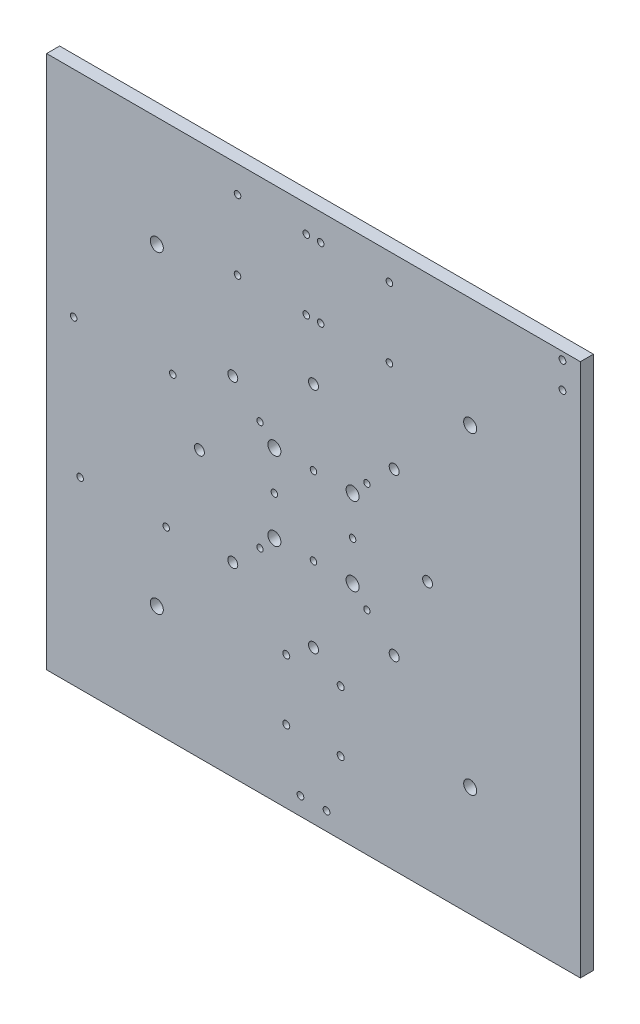
SolidWorks part; units mm, degrees
ref_plane "Front Plane" through (0, 0, 0) normal (0, 0, 1) x (1, 0, 0)
ref_plane "Top Plane" through (0, 0, 0) normal (0, 1, 0) x (1, 0, 0)
ref_plane "Right Plane" through (0, 0, 0) normal (1, 0, 0) x (0, 0, -1)
sketch "Sketch1" plane through (0, 0, 0) normal (0, 0, 1) x (1, 0, 0)
  line L0 (-130, 130) -> (130, 130)
  line L1 (130, 130) -> (130, -130)
  line L2 (130, -130) -> (-130, -130)
  line L3 (-130, -130) -> (-130, 130)
  line L4 (-120, 33.6598) -> (-120, -33.6505)
  line L5 (-29, 8) -> (-29, -8)
  line L6 (-29, 8) -> (-26.035, 8)
  line L7 (-26.035, 8) -> (-26.035, -8)
  line L8 (32.385, 33.02) -> (-32.385, 33.02)
  line L9 (-26.035, -8) -> (-29, -8)
  line L10 (-32.385, 33.02) -> (-32.385, -33.02)
  line L11 (-32.385, -33.02) -> (32.385, -33.02)
  line L12 (32.385, -33.02) -> (32.385, 33.02)
  line L13 (-107.2982, -46.3523) -> (-77.9253, -46.3523)
  line L14 (-113.65, 40.0098) -> (-71.5759, 40.0098)
  line L15 (-79.4148, 40.0098) -> (-79.4148, 22.9992)
  line L16 (-65.2259, -33.6529) -> (-65.2259, 33.6598)
  line L17 (-79.4148, 22.9992) -> (-94.8974, 22.9992)
  line L18 (-40, 120) -> (40, 120)
  line L19 (-94.8974, 22.9992) -> (-94.8974, 40.0098)
  line L31 (-40, 120) -> (-40, 80)
  line L32 (-40, 80) -> (40, 80)
  line L33 (40, 80) -> (40, 120)
  line L34 (-35, 100) -> (-35, 114.5)
  line L35 (-35, 114.5) -> (-29, 114.5)
  line L36 (-29, 114.5) -> (-29, 85.5)
  line L37 (-29, 85.5) -> (-35, 85.5)
  line L38 (-35, 85.5) -> (-35, 100)
  line L46 (16.75, -63) -> (16.75, -97)
  line L49 (16.75, -97) -> (-16.75, -97)
  line L50 (-16.75, -97) -> (-16.75, -63)
  line L51 (-16.75, -63) -> (16.75, -63)
  line L56 (120, 41.2) -> (120, -41.2)
  line L57 (45, 41.2) -> (45, -41.2)
  line L58 (120, 41.2) -> (45, 41.2)
  line L60 (45, -41.2) -> (120, -41.2)
  circle A0 centre (-26.035, 26.67) radius 1.55
  circle A1 centre (-26.035, -26.67) radius 1.55
  circle A2 centre (26.035, 26.67) radius 1.55
  circle A3 centre (26.035, -26.67) radius 1.55
  circle A4 centre (-116.825, 25.4027) radius 1.5875
  circle A5 centre (-113.65, -40.6352) radius 1.5875
  arc A6 (-120, -33.6505) -> (-107.2982, -46.3523) centre (-107.2982, -33.6505) ccw
  arc A7 (-77.9253, -46.3523) -> (-65.2259, -33.6529) centre (-77.9253, -33.6529) ccw
  arc A8 (-113.65, 40.0098) -> (-120, 33.6598) centre (-113.65, 33.6598) ccw
  arc A9 (-65.2259, 33.6598) -> (-71.5759, 40.0098) centre (-71.5759, 33.6598) ccw
  circle A10 centre (-68.565, 25.4048) radius 1.5875
  circle A11 centre (-37, 117) radius 1.6
  circle A12 centre (-37, 83) radius 1.6
  circle A13 centre (-3.5, 117) radius 1.6
  circle A14 centre (-3.5, 83) radius 1.6
  circle A15 centre (3.5, 117) radius 1.6
  circle A16 centre (37, 117) radius 1.6
  circle A17 centre (37, 83) radius 1.6
  circle A18 centre (3.5, 83) radius 1.6
  circle A19 centre (-13.25, -65.25) radius 1.7
  circle A20 centre (13.25, -65.25) radius 1.7
  circle A21 centre (13.25, -94.75) radius 1.7
  circle A22 centre (-13.25, -94.75) radius 1.7
  circle A23 centre (-76.33, 76.33) radius 3.175
  circle A24 centre (0, 55.575) radius 2.415
  circle A25 centre (-55.575, 0) radius 2.415
  circle A26 centre (0, -55.575) radius 2.415
  circle A27 centre (55.575, 0) radius 2.415
  circle A28 centre (-39.2975, 39.2975) radius 2.415
  circle A29 centre (39.2975, 39.2975) radius 2.415
  circle A30 centre (39.2975, -39.2975) radius 2.415
  circle A31 centre (-39.2975, -39.2975) radius 2.415
  circle A32 centre (76.33, 76.33) radius 3.175
  circle A33 centre (76.33, -76.33) radius 3.175
  circle A34 centre (-76.33, -76.33) radius 3.175
  arc A35 (-2.4144, 55.5225) -> (-37.5531, 40.9676) centre (0, 0) ccw
  arc A36 (37.5531, 40.9676) -> (2.4144, 55.5225) centre (0, 0) ccw
  arc A37 (55.5225, 2.4144) -> (40.9676, 37.5531) centre (0, 0) ccw
  arc A38 (40.9676, -37.5531) -> (55.5225, -2.4144) centre (0, 0) ccw
  arc A39 (2.4144, -55.5225) -> (37.5531, -40.9676) centre (0, 0) ccw
  arc A40 (-37.5531, -40.9676) -> (-2.4144, -55.5225) centre (0, 0) ccw
  arc A41 (-55.5225, -2.4144) -> (-40.9676, -37.5531) centre (0, 0) ccw
  arc A42 (-40.9676, 37.5531) -> (-55.5225, 2.4144) centre (0, 0) ccw
  circle A43 centre (-71.74, -40.6352) radius 1.5875
  circle A44 centre (6.35, -121.3) radius 1.651
  circle A45 centre (-6.35, -121.3) radius 1.651
  circle A46 centre (121.3, 126.35) radius 1.651
  circle A47 centre (121.3, 113.65) radius 1.651
  point P127 (127.65, 120)
  point P128 (-120, -120)
  point P129 (0, -127.65)
extrude "Boss-Extrude2" add sketch "Sketch1" along normal blind 6.35 contours L0 L1 L2 L3 | A32 | A33 | A23 | A34 | A10 | A43 | A5 | A4 | A25 | A28 | A24 | A31 | A26 | A30 | A27 | A29 | A1 | A3 | A2 | A0 | A22 | A21 | A20 | A19 | A45 | A44 | A46 | A47 | A17 | A16 | A18 | A14 | A15 | A13 | A11 | A12
sketch "Sketch2" plane through (0, 0, 0) normal (0, 0, -1) x (-1, 0, 0)
  circle A0 centre (0, 19.05) radius 1.5875 construction
  circle A1 centre (-19.05, 0) radius 1.5875 construction
  circle A2 centre (19.05, 0) radius 1.5875 construction
  circle A3 centre (0, -19.05) radius 1.5875 construction
  circle A4 centre (0, 19.05) radius 1.5875
  circle A5 centre (-19.05, 0) radius 1.5875
  circle A6 centre (19.05, 0) radius 1.5875
  circle A7 centre (0, -19.05) radius 1.5875
extrude "Cut-Extrude1" cut sketch "Sketch2" against normal through all contours A5 | A7 | A6 | A4
sketch "Sketch3" plane through (0, 0, 0) normal (0, 0, -1) x (-1, 0, 0)
  circle A0 centre (-19.05, 19.05) radius 3.175 construction
  circle A1 centre (19.05, 19.05) radius 3.175 construction
  circle A2 centre (-19.05, -19.05) radius 3.175 construction
  circle A3 centre (19.05, -19.05) radius 3.175 construction
  circle A4 centre (-19.05, 19.05) radius 3.175
  circle A5 centre (19.05, 19.05) radius 3.175
  circle A6 centre (-19.05, -19.05) radius 3.175
  circle A7 centre (19.05, -19.05) radius 3.175
extrude "Cut-Extrude2" cut sketch "Sketch3" against normal through all contours A6 | A7 | A4 | A5
sketch "Sketch5" plane through (0, 0, 0) normal (0, 0, -1) x (-1, 0, 0)
  circle A0 centre (0, 0) radius 55.752 construction
